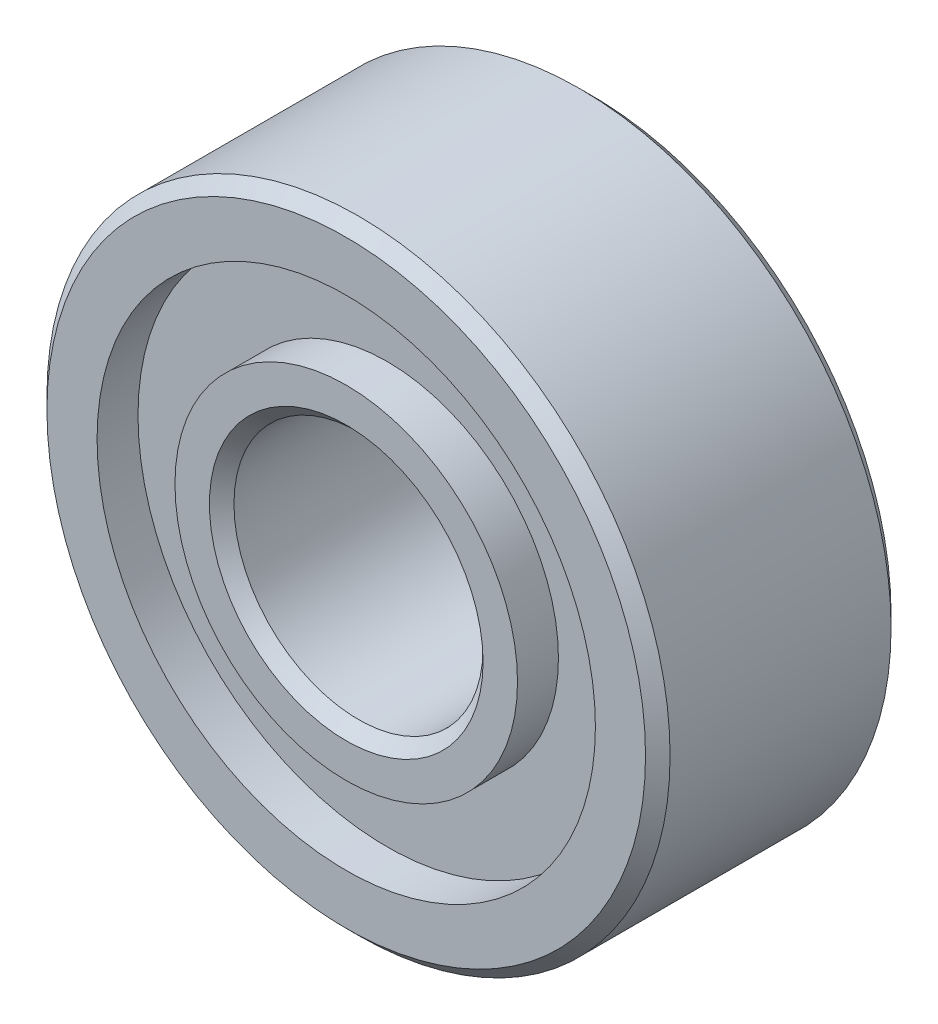
SolidWorks part; units mm, degrees
material "Alloy Steel"
ref_plane "Front Plane" through (0, 0, 0) normal (0, 0, 1) x (1, 0, 0)
ref_plane "Top Plane" through (0, 0, 0) normal (0, 1, 0) x (1, 0, 0)
ref_plane "Right Plane" through (0, 0, 0) normal (1, 0, 0) x (0, 0, -1)
ref_plane "Plane1" through (0, 0, 3.94) normal (0, 0, 1) x (1, 0, 0)
sketch "Sketch1" plane through (0, 0, 3.94) normal (0, 0, 1) x (1, 0, 0)
  circle A0 centre (0, 0) radius 5
  dimension "D1" = 10
extrude "Extrude1" add sketch "Sketch1" against normal blind 3.94
hole_wizard "Hole1" positions "Sketch3" profile "Sketch2" legacy
sketch "Sketch3" plane through (0, 0, 3.94) normal (0, 0, 1) x (1, 0, 0)
  point P0 (0, 0)
sketch "Sketch2" plane through (0, 0, 3.94) normal (1, 0, 0) x (0, -1, 0)
  line L0 (0, 0) -> (0, 0.6567)
  line L1 (0, 0.6567) -> (3.9984, 0.6567)
  line L2 (3.9984, 0.6567) -> (3.9984, 0)
  line L3 (3.9984, 0) -> (0, 0)
  line L4 (0, 110) -> (0, -10) construction
  dimension "Diameter" = 7.9968
  dimension "Depth" = 0.6567
sketch "Sketch4" plane through (0, 0, 3.2833) normal (0, 0, 1) x (1, 0, 0)
  circle A0 centre (0, 0) radius 2.7486
  dimension "D1" = 5.4972
extrude "Extrude2" add sketch "Sketch4" along normal blind 0.6567
hole_wizard "Hole2" positions "Sketch6" profile "Sketch5" legacy
sketch "Sketch6" plane through (0, 0, 0) normal (0, 0, -1) x (-1, 0, 0)
  point P0 (0, 0)
sketch "Sketch5" plane through (0, 0, 0) normal (1, 0, 0) x (0, 1, 0)
  line L0 (0, 0) -> (0, 0.6567)
  line L1 (0, 0.6567) -> (3.9984, 0.6567)
  line L2 (3.9984, 0.6567) -> (3.9984, 0)
  line L3 (3.9984, 0) -> (0, 0)
  line L4 (0, 110) -> (0, -10) construction
  dimension "Diameter" = 7.9968
  dimension "Depth" = 0.6567
sketch "Sketch7" plane through (0, 0, 0.6567) normal (0, 0, -1) x (-1, 0, 0)
  circle A0 centre (0, 0) radius 2.7486
  dimension "D1" = 5.4972
extrude "Extrude3" add sketch "Sketch7" along normal blind 0.6567
hole_wizard "Hole3" positions "Sketch9" profile "Sketch8" legacy
sketch "Sketch9" plane through (0, 0, 0) normal (0, 0, -1) x (-1, 0, 0)
  point P0 (0, 0)
sketch "Sketch8" plane through (0, 0, 0) normal (1, 0, 0) x (0, 1, 0)
  line L0 (0, 0) -> (0, 3.94)
  line L1 (0, 3.94) -> (1.9988, 3.94)
  line L2 (1.9988, 3.94) -> (1.9988, 0)
  line L3 (1.9988, 0) -> (0, 0)
  line L4 (0, 110) -> (0, -10) construction
  dimension "Diameter" = 3.9975
  dimension "Depth" = 3.94
chamfer "Chamfer1" distance 0.197 angle 45 4 edges at (-1.9988, 0, 0) (-5, 0, 0) (-5, 0, 3.94) (1.9988, 0, 3.94)
